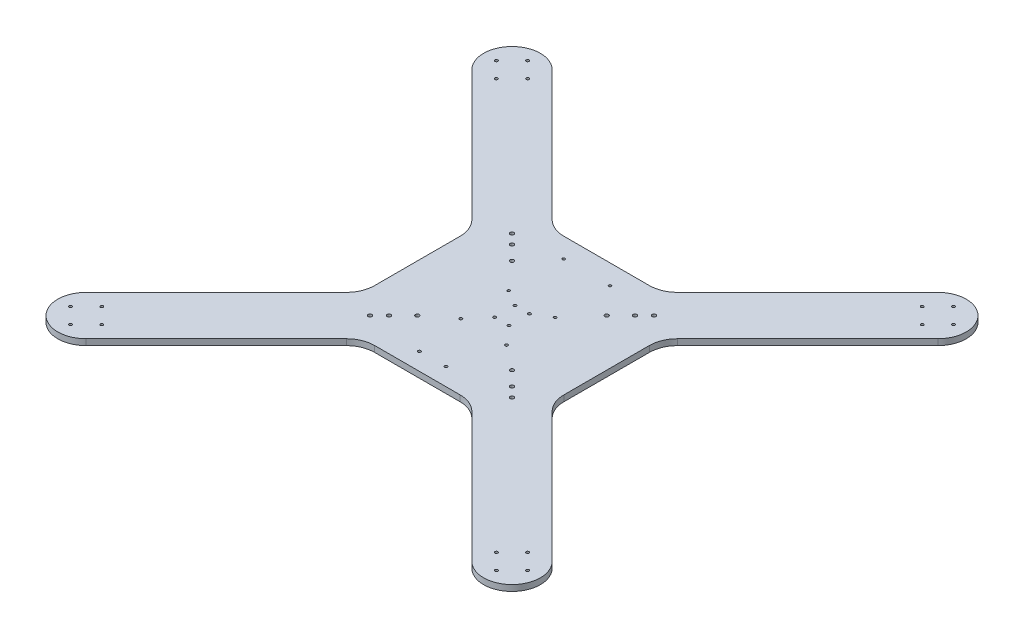
SolidWorks part; units mm, degrees
ref_plane "Front Plane" through (0, 0, 0) normal (0, 0, 1) x (1, 0, 0)
ref_plane "Top Plane" through (0, 0, 0) normal (0, 1, 0) x (1, 0, 0)
ref_plane "Right Plane" through (0, 0, 0) normal (1, 0, 0) x (0, 0, -1)
sketch "Sketch1" plane through (0, 0, 0) normal (0, 1, 0) x (1, 0, 0)
  line L0 (0, 144.0829) -> (0, -147.1815) construction
  line L1 (-89.1771, 89.1771) -> (-103.0994, 103.0994) construction
  line L2 (-141.5008, 0) -> (145.1158, 0) construction
  line L3 (-246.1892, 203.7628) -> (-108.7868, 66.3604)
  line L4 (-100, -45.1472) -> (-100, 45.1472)
  line L5 (-45.1472, 100) -> (45.1472, 100)
  line L6 (-203.7868, 246.2132) -> (-66.3604, 108.7868)
  line L7 (-45.1472, -100) -> (45.1472, -100)
  line L8 (-203.7868, -246.2132) -> (-66.3604, -108.7868)
  line L9 (-246.1892, -203.7628) -> (-108.7868, -66.3604)
  line L10 (203.7868, 246.2132) -> (66.3604, 108.7868)
  line L11 (246.1892, 203.7628) -> (108.7868, 66.3604)
  line L12 (100, -45.1472) -> (100, 45.1472)
  line L13 (203.7868, -246.2132) -> (66.3604, -108.7868)
  line L14 (246.1892, -203.7628) -> (108.7868, -66.3604)
  arc A0 (-203.7868, 246.2132) -> (-246.1892, 203.7628) centre (-225, 225) ccw
  arc A1 (-45.1472, 100) -> (-66.3604, 108.7868) centre (-45.1472, 130) cw
  arc A2 (-100, 45.1472) -> (-108.7868, 66.3604) centre (-130, 45.1472) ccw
  arc A3 (-45.1472, -100) -> (-66.3604, -108.7868) centre (-45.1472, -130) ccw
  arc A4 (-203.7868, -246.2132) -> (-246.1892, -203.7628) centre (-225, -225) cw
  arc A5 (-100, -45.1472) -> (-108.7868, -66.3604) centre (-130, -45.1472) cw
  arc A6 (45.1472, 100) -> (66.3604, 108.7868) centre (45.1472, 130) ccw
  arc A7 (203.7868, 246.2132) -> (246.1892, 203.7628) centre (225, 225) cw
  arc A8 (100, 45.1472) -> (108.7868, 66.3604) centre (130, 45.1472) cw
  arc A9 (100, -45.1472) -> (108.7868, -66.3604) centre (130, -45.1472) ccw
  arc A10 (45.1472, -100) -> (66.3604, -108.7868) centre (45.1472, -130) cw
  arc A11 (203.7868, -246.2132) -> (246.1892, -203.7628) centre (225, -225) ccw
  point P16 (0, 0)
  point P29 (-100, 0)
  point P30 (0, 100)
  point P42 (0, -100)
  dimension "D1" = 60
  dimension "D7" = 225
  dimension "D8" = 225
  dimension "D9" = 30
  dimension "D10" = 30
  dimension "D2" = 45
  dimension "D3" = 100
  dimension "D4" = 100
  dimension "D5" = 45
  dimension "D6" = 45
extrude "Boss-Extrude1" add sketch "Sketch1" along normal blind 6.35
sketch "Sketch2" plane through (0, 6.35, 0) normal (0, 1, 0) x (1, 0, 0)
  line L0 (0, 276.6181) -> (0, -241.8402) construction
  line L2 (-234.8196, 0) -> (254.7802, 0) construction
  line L4 (-13.469, 13.469) -> (-391.0681, 391.0681) construction
  line L5 (-225, 225) -> (-225, 241.5) construction
  circle A0 centre (-225, 225) radius 16.5 construction
  circle A1 centre (-225, 241.5) radius 1.5
  circle A2 centre (-208.5, 225) radius 1.5
  circle A3 centre (-225, 208.5) radius 1.5
  circle A4 centre (-241.5, 225) radius 1.5
  circle A5 centre (241.5, 225) radius 1.5
  circle A6 centre (225, 241.5) radius 1.5
  circle A7 centre (208.5, 225) radius 1.5
  circle A8 centre (225, 208.5) radius 1.5
  circle A9 centre (225, -241.5) radius 1.5
  circle A10 centre (241.5, -225) radius 1.5
  circle A11 centre (225, -208.5) radius 1.5
  circle A12 centre (208.5, -225) radius 1.5
  circle A13 centre (-241.5, -225) radius 1.5
  circle A14 centre (-225, -241.5) radius 1.5
  circle A15 centre (-208.5, -225) radius 1.5
  circle A16 centre (-225, -208.5) radius 1.5
  point P3 (-225, 225)
  point P22 (-225, 225)
  point P47 (0, 0)
  dimension "D4" = 4
  dimension "D1" = 45
  dimension "D2" = 225
  dimension "D3" = 225
  dimension "D5" = 4
extrude "Cut-Extrude1" cut sketch "Sketch2" against normal blind 212
sketch "Sketch3" plane through (0, 6.35, 0) normal (0, 1, 0) x (1, 0, 0)
  line L0 (0, 50.2466) -> (0, -56.289) construction
  line L6 (-89.0638, 0) -> (75.0494, 0) construction
  line L8 (0, 10.795) -> (-7.62, 10.795) construction
  line L9 (-7.62, 10.795) -> (-7.62, 0) construction
  circle A0 centre (-7.62, 10.795) radius 1.5
  circle A1 centre (-7.62, -10.795) radius 1.5
  circle A2 centre (7.62, -10.795) radius 1.5
  circle A3 centre (7.62, 10.795) radius 1.5
  dimension "D1" = 7.62
  dimension "D2" = 10.795
extrude "Cut-Extrude2" cut sketch "Sketch3" against normal blind 212
sketch "Sketch4" plane through (0, 6.35, 0) normal (0, 1, 0) x (1, 0, 0)
  line L0 (0, 107.0637) -> (0, -25.5859) construction
  line L2 (-141.7917, 0) -> (125.279, 0) construction
  line L4 (63.494, 50) -> (-58.0829, 50) construction
  line L5 (-24.5, 50) -> (-24.5, 21) construction
  line L6 (-24.5, 21) -> (0, 21) construction
  circle A0 centre (-24.5, 21) radius 1.375
  circle A1 centre (24.5, 21) radius 1.375
  circle A2 centre (24.5, 79) radius 1.375
  circle A3 centre (-24.5, 79) radius 1.375
  dimension "D1" = 50
  dimension "D2" = 24.5
  dimension "D3" = 29
extrude "Cut-Extrude3" cut sketch "Sketch4" against normal blind 212
sketch "Sketch5" plane through (0, 6.35, 0) normal (0, 1, 0) x (1, 0, 0)
  line L0 (0, 190.7934) -> (0, -190.1204) construction
  line L2 (-258.5557, 0) -> (324.2632, 0) construction
  line L4 (-161.3876, -30) -> (142.753, -30) construction
  line L5 (24.15, -30) -> (11.8579, -81.5549) construction
  line L6 (11.8579, -81.5549) -> (-16.1418, -81.6833) construction
  line L7 (-16.1418, -81.6833) -> (-24.15, -30) construction
  circle A0 centre (24.15, -30) radius 1.5
  circle A1 centre (-24.15, -30) radius 1.5
  circle A2 centre (-16.1418, -81.6833) radius 1.5
  circle A3 centre (11.8579, -81.5549) radius 1.5
  dimension "D2" = 24.15
  dimension "D1" = 30
  dimension "D3" = 52.3
  dimension "D4" = 28
  dimension "D5" = 53
extrude "Cut-Extrude4" cut sketch "Sketch5" against normal blind 212
sketch "Sketch6" plane through (0, 6.35, 0) normal (0, 1, 0) x (1, 0, 0)
  line L0 (41.7136, 100) -> (-52.9655, 100) construction
  line L1 (-3.4925, 0) -> (3.4925, 0) construction
  line L2 (-100, 31.0423) -> (-100, -31.8978) construction
  line L3 (0, -3.4925) -> (0, 3.4925) construction
  line L4 (-35.7511, -100) -> (25.5751, -100) construction
  line L6 (100, 33.732) -> (100, -25.9803) construction
  line L8 (0, 0) -> (100, 100) construction
  circle A0 centre (75, 75) radius 2
  circle A1 centre (65, 65) radius 2
  circle A2 centre (50, 50) radius 2
  circle A3 centre (50, -50) radius 2
  circle A4 centre (65, -65) radius 2
  circle A5 centre (75, -75) radius 2
  circle A6 centre (-50, -50) radius 2
  circle A7 centre (-65, -65) radius 2
  circle A8 centre (-75, -75) radius 2
  circle A9 centre (-50, 50) radius 2
  circle A10 centre (-65, 65) radius 2
  circle A11 centre (-75, 75) radius 2
  point P42 (0, 0)
  dimension "D1" = 75
  dimension "D3" = 65
  dimension "D4" = 50
  dimension "D2" = 45
  dimension "D5" = 4
extrude "Cut-Extrude5" cut sketch "Sketch6" against normal blind 212
